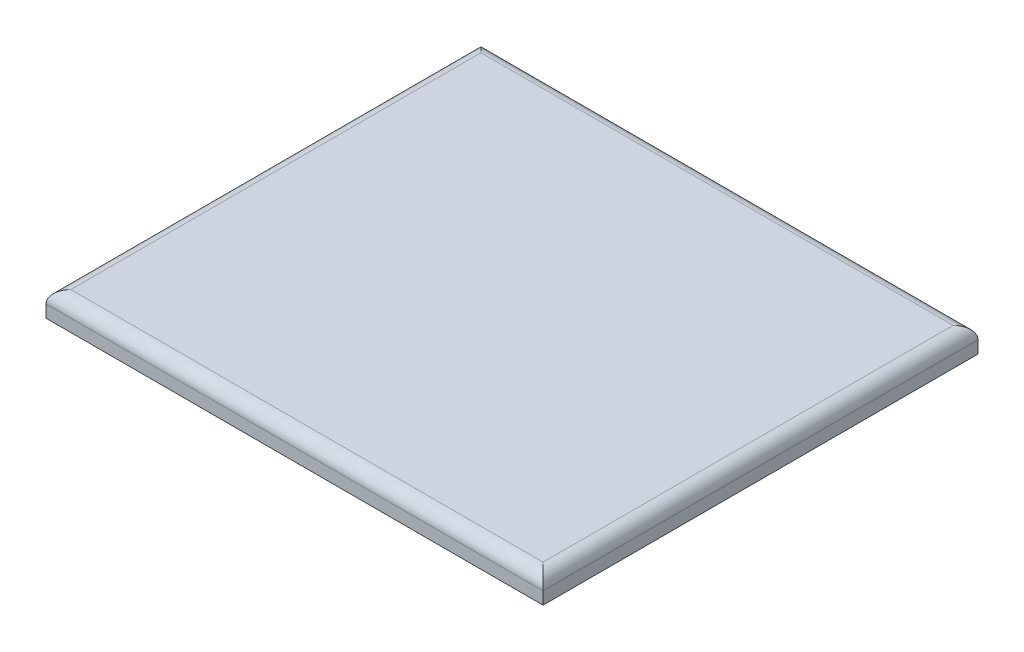
SolidWorks part; units mm, degrees
material "Polyurethane Foam Flexible"
ref_plane "Front Plane" through (0, 0, 0) normal (0, 0, 1) x (1, 0, 0)
ref_plane "Top Plane" through (0, 0, 0) normal (0, 1, 0) x (1, 0, 0)
ref_plane "Right Plane" through (0, 0, 0) normal (1, 0, 0) x (0, 0, -1)
sketch "Sketch1" plane through (0, 0, 0) normal (0, 1, 0) x (1, 0, 0)
  line L1 (-200, -175) -> (200, -175)
  line L2 (-200, -175) -> (-200, 175)
  line L3 (-200, 175) -> (200, 175)
  line L4 (200, -175) -> (200, 175)
  line L5 (-200, -175) -> (200, 175) construction
  line L6 (-200, 175) -> (200, -175) construction
  point P0 (0, 0)
  dimension "D1" = 400
  dimension "D2" = 350
extrude "Boss-Extrude1" add sketch "Sketch1" along normal blind 20
fillet "Fillet1" radius 10 4 edges at (0, 20, 175) (-200, 20, 0) (0, 20, -175) (200, 20, 0)
